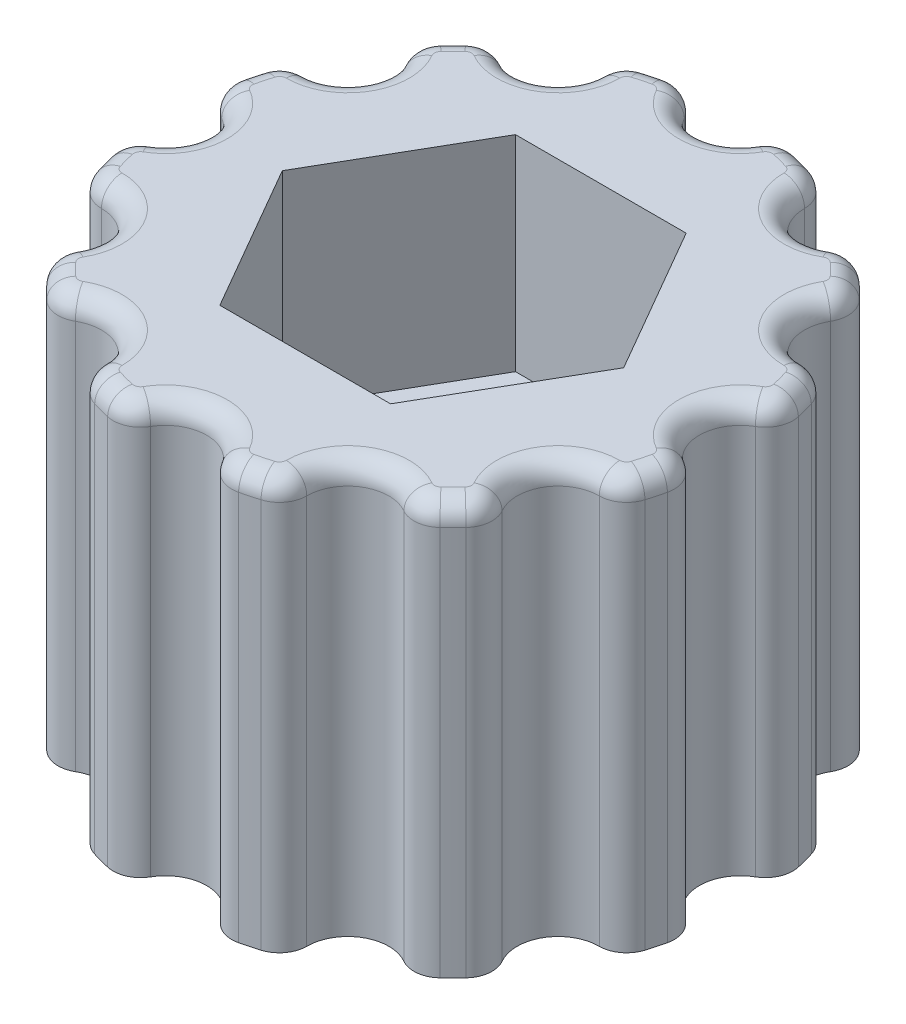
SolidWorks part; units mm, degrees
ref_plane "Front Plane" through (0, 0, 0) normal (0, 0, 1) x (1, 0, 0)
ref_plane "Top Plane" through (0, 0, 0) normal (0, 1, 0) x (1, 0, 0)
ref_plane "Right Plane" through (0, 0, 0) normal (1, 0, 0) x (0, 0, -1)
sketch "Sketch1" plane through (0, 0, 0) normal (0, 1, 0) x (1, 0, 0)
  circle A0 centre (0, 0) radius 3.5 construction
  circle A1 centre (0, 0) radius 7
  dimension "D1" = 7
  dimension "D2" = 14
extrude "Body" add sketch "Sketch1" along normal blind 10
ref_plane "Top of Knob Sketch Plane" through (0, 10, 0) normal (0, 1, 0) x (1, 0, 0)
sketch "Sketch2" plane through (0, 10, 0) normal (0, 1, 0) x (1, 0, 0)
  circle A0 centre (0, 0) radius 2.2
  dimension "D1" = 4.4
extrude "Mounting Hole" cut sketch "Sketch2" against normal up to next
sketch "Sketch3" plane through (0, 10, 0) normal (0, 1, 0) x (1, 0, 0)
  line L1 (2.0785, 3.6) -> (-2.0785, 3.6)
  line L2 (-2.0785, 3.6) -> (-4.1569, 0)
  line L3 (-4.1569, 0) -> (-2.0785, -3.6)
  line L4 (-2.0785, -3.6) -> (2.0785, -3.6)
  line L5 (2.0785, -3.6) -> (4.1569, 0)
  line L6 (4.1569, 0) -> (2.0785, 3.6)
  circle A0 centre (0, 0) radius 3.6 construction
  dimension "D1" = 7.2
extrude "Nut Counterbore" cut sketch "Sketch3" against normal blind 5
sketch "Sketch5" plane through (0, 10, 0) normal (0, 1, 0) x (1, 0, 0)
  line L0 (0, 0.4356) -> (0, 8.2303) construction
  line L1 (-0.866, 6.5) -> (0.866, 6.5) construction
  line L2 (-1.4434, 6.1667) -> (0, 7) construction
  line L3 (0, 7) -> (1.4434, 6.1667) construction
  circle A0 centre (0, 0) radius 7 construction
  arc A1 (-0.866, 6.5) -> (0.866, 6.5) centre (0, 7) ccw
  arc A2 (0.866, 6.5) -> (1.5953, 6.8158) centre (1.4434, 6.1667) cw
  arc A3 (-0.866, 6.5) -> (-1.5953, 6.8158) centre (-1.4434, 6.1667) ccw
  arc A4 (-1.5953, 6.8158) -> (1.5953, 6.8158) centre (0, 0) cw
  arc A5 (2.5, 6.0622) -> (4, 5.1962) centre (3.5, 6.0622) ccw
  arc A6 (2.5, 6.0622) -> (2.0263, 6.7003) centre (1.8333, 6.0622) ccw
  arc A7 (2.0263, 6.7003) -> (4.7895, 5.105) centre (0, 0) cw
  arc A8 (4, 5.1962) -> (4.7895, 5.105) centre (4.3333, 4.6188) cw
  arc A9 (5.1962, 4) -> (6.0622, 2.5) centre (6.0622, 3.5) ccw
  arc A10 (5.1962, 4) -> (5.105, 4.7895) centre (4.6188, 4.3333) ccw
  arc A11 (5.105, 4.7895) -> (6.7003, 2.0263) centre (0, 0) cw
  arc A12 (6.0622, 2.5) -> (6.7003, 2.0263) centre (6.0622, 1.8333) cw
  arc A13 (6.5, 0.866) -> (6.5, -0.866) centre (7, 0) ccw
  arc A14 (6.5, 0.866) -> (6.8158, 1.5953) centre (6.1667, 1.4434) ccw
  arc A15 (6.8158, 1.5953) -> (6.8158, -1.5953) centre (0, 0) cw
  arc A16 (6.5, -0.866) -> (6.8158, -1.5953) centre (6.1667, -1.4434) cw
  arc A17 (6.0622, -2.5) -> (5.1962, -4) centre (6.0622, -3.5) ccw
  arc A18 (6.0622, -2.5) -> (6.7003, -2.0263) centre (6.0622, -1.8333) ccw
  arc A19 (6.7003, -2.0263) -> (5.105, -4.7895) centre (0, 0) cw
  arc A20 (5.1962, -4) -> (5.105, -4.7895) centre (4.6188, -4.3333) cw
  arc A21 (4, -5.1962) -> (2.5, -6.0622) centre (3.5, -6.0622) ccw
  arc A22 (4, -5.1962) -> (4.7895, -5.105) centre (4.3333, -4.6188) ccw
  arc A23 (4.7895, -5.105) -> (2.0263, -6.7003) centre (0, 0) cw
  arc A24 (2.5, -6.0622) -> (2.0263, -6.7003) centre (1.8333, -6.0622) cw
  arc A25 (0.866, -6.5) -> (-0.866, -6.5) centre (0, -7) ccw
  arc A26 (0.866, -6.5) -> (1.5953, -6.8158) centre (1.4434, -6.1667) ccw
  arc A27 (1.5953, -6.8158) -> (-1.5953, -6.8158) centre (0, 0) cw
  arc A28 (-0.866, -6.5) -> (-1.5953, -6.8158) centre (-1.4434, -6.1667) cw
  arc A29 (-2.5, -6.0622) -> (-4, -5.1962) centre (-3.5, -6.0622) ccw
  arc A30 (-2.5, -6.0622) -> (-2.0263, -6.7003) centre (-1.8333, -6.0622) ccw
  arc A31 (-2.0263, -6.7003) -> (-4.7895, -5.105) centre (0, 0) cw
  arc A32 (-4, -5.1962) -> (-4.7895, -5.105) centre (-4.3333, -4.6188) cw
  arc A33 (-5.1962, -4) -> (-6.0622, -2.5) centre (-6.0622, -3.5) ccw
  arc A34 (-5.1962, -4) -> (-5.105, -4.7895) centre (-4.6188, -4.3333) ccw
  arc A35 (-5.105, -4.7895) -> (-6.7003, -2.0263) centre (0, 0) cw
  arc A36 (-6.0622, -2.5) -> (-6.7003, -2.0263) centre (-6.0622, -1.8333) cw
  arc A37 (-6.5, -0.866) -> (-6.5, 0.866) centre (-7, 0) ccw
  arc A38 (-6.5, -0.866) -> (-6.8158, -1.5953) centre (-6.1667, -1.4434) ccw
  arc A39 (-6.8158, -1.5953) -> (-6.8158, 1.5953) centre (0, 0) cw
  arc A40 (-6.5, 0.866) -> (-6.8158, 1.5953) centre (-6.1667, 1.4434) cw
  arc A41 (-6.0622, 2.5) -> (-5.1962, 4) centre (-6.0622, 3.5) ccw
  arc A42 (-6.0622, 2.5) -> (-6.7003, 2.0263) centre (-6.0622, 1.8333) ccw
  arc A43 (-6.7003, 2.0263) -> (-5.105, 4.7895) centre (0, 0) cw
  arc A44 (-5.1962, 4) -> (-5.105, 4.7895) centre (-4.6188, 4.3333) cw
  arc A45 (-4, 5.1962) -> (-2.5, 6.0622) centre (-3.5, 6.0622) ccw
  arc A46 (-4, 5.1962) -> (-4.7895, 5.105) centre (-4.3333, 4.6188) ccw
  arc A47 (-4.7895, 5.105) -> (-2.0263, 6.7003) centre (0, 0) cw
  arc A48 (-2.5, 6.0622) -> (-2.0263, 6.7003) centre (-1.8333, 6.0622) cw
  point P94 (0, 0)
  dimension "D2" = 1
  dimension "D1" = 120
  dimension "D3" = 12
extrude "Knurl Cutting Tool" cut sketch "Sketch5" against normal through all
fillet "Fillet1" radius 0.5 48 edges at (-4.9497, 10, -4.9497) (-5.2811, 10, -4.4098) (-5.1962, 10, -3) (-6.4595, 10, -2.3686) (-6.7615, 10, -1.8117) (-6.7784, 10, -1.1785) (-6, 10, 0) (-6.7784, 10, 1.1785) (-6.7615, 10, 1.8117) (-6.4595, 10, 2.3686) (-5.1962, 10, 3) (-5.2811, 10, 4.4098) (-4.9497, 10, 4.9497) (-4.4098, 10, 5.2811) (-3, 10, 5.1962) (-2.3686, 10, 6.4595) (-1.8117, 10, 6.7615) (-1.1785, 10, 6.7784) (0, 10, 6) (1.1785, 10, 6.7784) (1.8117, 10, 6.7615) (2.3686, 10, 6.4595) (3, 10, 5.1962) (4.4098, 10, 5.2811) (4.9497, 10, 4.9497) (5.2811, 10, 4.4098) (5.1962, 10, 3) (6.4595, 10, 2.3686) (6.7615, 10, 1.8117) (6.7784, 10, 1.1785) (6, 10, 0) (6.7784, 10, -1.1785) (6.7615, 10, -1.8117) (6.4595, 10, -2.3686) (5.1962, 10, -3) (5.2811, 10, -4.4098) (4.9497, 10, -4.9497) (4.4098, 10, -5.2811) (3, 10, -5.1962) (2.3686, 10, -6.4595) (1.8117, 10, -6.7615) (1.1785, 10, -6.7784) (0, 10, -6) (-1.1785, 10, -6.7784) (-1.8117, 10, -6.7615) (-2.3686, 10, -6.4595) (-3, 10, -5.1962) (-4.4098, 10, -5.2811)
equation "\"Depth\"= 10mm"
equation "\"D1@Top of Knob Sketch Plane\"=\"Depth\""
